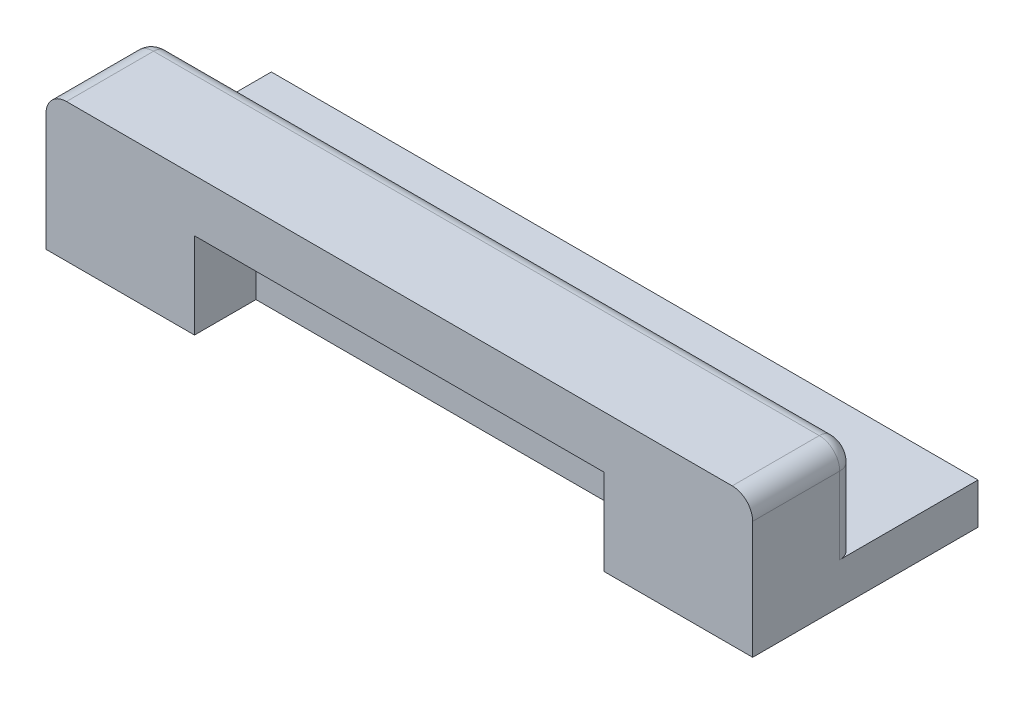
SolidWorks part; units mm, degrees
ref_plane "Front Plane" through (0, 0, 0) normal (0, 0, 1) x (1, 0, 0)
ref_plane "Top Plane" through (0, 0, 0) normal (0, 1, 0) x (1, 0, 0)
ref_plane "Right Plane" through (0, 0, 0) normal (1, 0, 0) x (0, 0, -1)
sketch "Sketch1" plane through (0, 0, 0) normal (0, 1, 0) x (1, 0, 0)
  line L1 (34.5, 11) -> (-34.5, 11)
  line L2 (34.5, 11) -> (34.5, -11)
  line L3 (34.5, -11) -> (-34.5, -11)
  line L4 (-34.5, 11) -> (-34.5, -11)
  line L5 (34.5, 11) -> (-34.5, -11) construction
  line L6 (34.5, -11) -> (-34.5, 11) construction
  point P0 (0, 0)
  dimension "D1" = 69
  dimension "D2" = 22
extrude "Boss-Extrude1" add sketch "Sketch1" along normal blind 3 and the other way blind 1
sketch "Sketch2" plane through (0, 3, 0) normal (0, 1, 0) x (1, 0, 0)
  line L1 (-34.5, -11) -> (-21.5, -11)
  line L2 (-34.5, -11) -> (-34.5, -1)
  line L3 (-34.5, -1) -> (-21.5, -1)
  line L5 (34.5, -11) -> (21.5, -11)
  line L6 (34.5, -11) -> (34.5, -1)
  line L7 (34.5, -1) -> (21.5, -1)
  line L9 (-21.5, -1) -> (21.5, -1)
  line L11 (-21.5, -11) -> (21.5, -11)
  dimension "D5" = 10
extrude "Boss-Extrude2" add sketch "Sketch2" along normal blind 9.5
ref_plane "Plane1" through (31.5, 0, 0) normal (1, 0, 0) x (0, 0, -1)
sketch "Sketch4" plane through (31.5, 0, 0) normal (1, 0, 0) x (0, 0, -1)
  line L0 (-1, 3) -> (-3.5, 7.5)
  line L2 (-1, 3) -> (-1, 7.5)
  line L3 (-1, 7.5) -> (-3.5, 7.5)
  line L5 (-11, 12.5) -> (-1, 12.5) construction
  dimension "D1" = 5
  dimension "D2" = 2.5
extrude "Cut-Extrude2" cut sketch "Sketch4" against normal blind 63 contours L2 L3 L0
sketch "Sketch5" plane through (0, 0, 11) normal (0, 0, 1) x (1, 0, 0)
  line L0 (-34.5, -1) -> (34.5, -1) construction
  line L1 (20, -1) -> (-20, -1)
  line L2 (20, -1) -> (20, 7.4)
  line L3 (20, 7.4) -> (-20, 7.4)
  line L4 (-20, -1) -> (-20, 7.4)
  line L5 (0, 0) -> (0, 19.3767) construction
  dimension "D1" = 40
  dimension "D2" = 8.4
extrude "Cut-Extrude3" cut sketch "Sketch5" against normal blind 6
fillet "Fillet5" radius 2 2 edges at (-34.5, 12.5, 6) (34.5, 12.5, 6)
fillet "Fillet6" radius 1.5 5 edges at (34.5, 6.75, 1) (33.9142, 11.9142, 1) (-34.5, 6.75, 1) (-33.9142, 11.9142, 1) (0, 12.5, 1)
